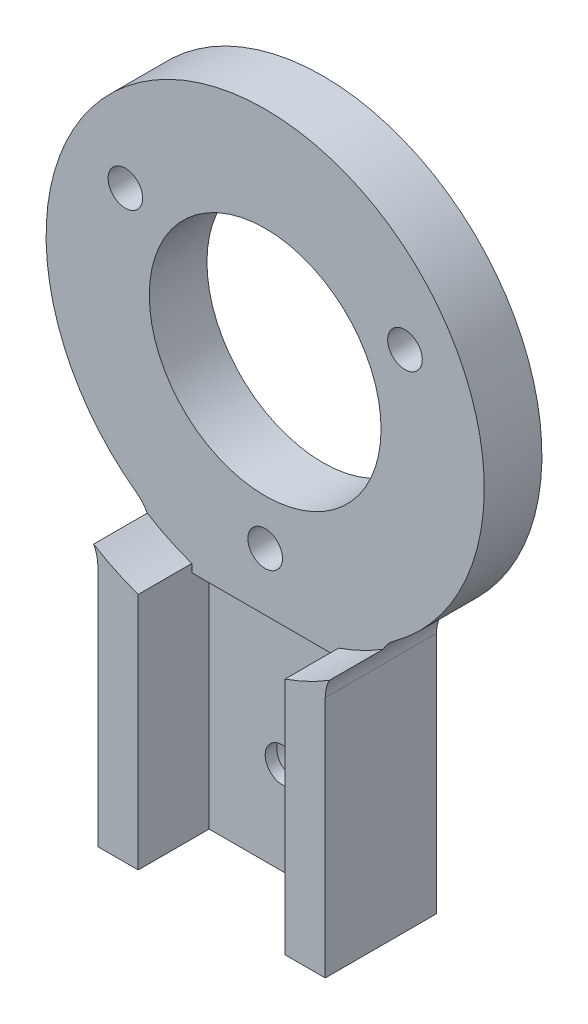
SolidWorks part; units mm, degrees
ref_plane "Front Plane" through (0, 0, 0) normal (0, 0, 1) x (1, 0, 0)
ref_plane "Top Plane" through (0, 0, 0) normal (0, 1, 0) x (1, 0, 0)
ref_plane "Right Plane" through (0, 0, 0) normal (1, 0, 0) x (0, 0, -1)
sketch "Sketch1" plane through (0, 0, 0) normal (0, 0, 1) x (1, 0, 0)
  line L0 (0, -19) -> (0, -39) construction
  line L1 (9.86, -39) -> (-9.86, -39)
  line L2 (-9.86, -39) -> (-9.86, -16.2413)
  line L3 (9.86, -39) -> (9.86, -16.2413)
  line L4 (6.36, -30.5545) -> (-6.36, -30.5545) construction
  circle A0 centre (0, 0) radius 19 construction
  circle A1 centre (0, 0) radius 10
  arc A2 (-9.86, -16.2413) -> (9.86, -16.2413) centre (0, 0) cw
  point P11 (0, -39)
  point P14 (0, -30.5545)
  dimension "D1" = 38
  dimension "D2" = 20
  dimension "D3" = 12.72
  dimension "D4" = 3.5
  dimension "D5" = 20
extrude "Boss-Extrude1" add sketch "Sketch1" along normal blind 5
sketch "Sketch6" plane through (0, 0, 5) normal (0, 0, 1) x (1, 0, 0)
  circle A0 centre (0, 0) radius 19 construction
sketch "Sketch5" plane through (0, -39, 0) normal (0, -1, 0) x (1, 0, 0)
  line L1 (0, 0) -> (0, 3.5) construction
  line L2 (-9.86, 0) -> (9.86, 0) construction
  line L3 (6.36, 3.5) -> (-6.36, 3.5)
  line L4 (-6.36, 3.5) -> (-6.36, 5)
  line L5 (-9.86, 5) -> (9.86, 5) construction
  line L6 (-6.36, 5) -> (6.36, 5)
  line L7 (6.36, 5) -> (6.36, 3.5)
  dimension "D1" = 3.5
  dimension "D2" = 12.72
extrude "Cut-Extrude1" cut sketch "Sketch5" against normal blind 20
sketch "Sketch7" plane through (0, -39, 0) normal (0, -1, 0) x (1, 0, 0)
  line L0 (0, 3.5) -> (0, 9.86) construction
  line L1 (-6.36, 3.5) -> (6.36, 3.5) construction
  dimension "D1" = 6.36
ref_plane "Plane2" through (0, 0, 9.86) normal (0, 0, 1) x (1, 0, 0)
sketch "Sketch8" plane through (0, 0, 9.86) normal (0, 0, 1) x (1, 0, 0)
  line L0 (0, -39) -> (0, 0) construction
sketch "Sketch18" plane through (0, 0, 5) normal (0, 0, 1) x (1, 0, 0)
  line L0 (0, -14) -> (0, 0) construction
  line L1 (0, 0) -> (-12.1244, 7) construction
  line L3 (12.1244, 7) -> (0, 0) construction
  circle A0 centre (0, 0) radius 14 construction
  circle A1 centre (0, -14) radius 1.5
  circle A2 centre (-12.1244, 7) radius 1.5
  circle A3 centre (12.1244, 7) radius 1.5
  dimension "D1" = 28
  dimension "D2" = 3
  dimension "D3" = 120
  dimension "D4" = 120
extrude "Cut-Extrude6" cut sketch "Sketch18" against normal through all
sketch "Sketch10" plane through (0, 0, 5) normal (0, 0, 1) x (1, 0, 0)
  line L0 (9.86, -39) -> (9.86, -16.2413) construction
  line L1 (-9.86, -39) -> (-6.36, -39)
  line L2 (-9.86, -39) -> (-9.86, -19)
  line L3 (-9.86, -19) -> (-6.36, -19)
  line L4 (-6.36, -39) -> (-6.36, -19)
  line L5 (6.36, -39) -> (9.86, -39)
  line L6 (6.36, -39) -> (6.36, -19)
  line L7 (6.36, -19) -> (9.86, -19)
  line L8 (9.86, -39) -> (9.86, -19)
extrude "Boss-Extrude3" add sketch "Sketch10" along normal offset from surface (4.65 mm away) 9.65 up to face at (13.6244, 7, 0)
sketch "Sketch15" plane through (0, 0, 0) normal (0, 0, -1) x (-1, 0, 0)
  circle A0 centre (0, -14) radius 3
  circle A1 centre (-12.1244, 7) radius 3
  circle A2 centre (12.1244, 7) radius 3
  dimension "D1" = 6
extrude "Cut-Extrude4" cut sketch "Sketch15" against normal blind 2.5
sketch "Sketch19" plane through (0, 0, 0) normal (0, 0, -1) x (-1, 0, 0)
  circle A0 centre (0, 0) radius 10.05
  dimension "D1" = 20.1
extrude "Cut-Extrude7" cut sketch "Sketch19" against normal through all
sketch "Sketch23" plane through (0, 0, 5) normal (0, 0, 1) x (1, 0, 0)
  line L0 (9.86, -16.6785) -> (9.86, -19)
  line L1 (9.86, -19) -> (6.36, -19)
  line L2 (6.36, -19) -> (6.36, -18.3014)
  arc A0 (6.36, -18.3014) -> (9.86, -16.6785) centre (0, 0) ccw
  dimension "D1" = 38.75
extrude "Boss-Extrude6" add sketch "Sketch23" along normal up to surface (4.65 mm away) up to face at (8.11, -29, 9.65)
mirror "Mirror1" about plane through (0, 0, 0) normal (1, 0, 0) of "Boss-Extrude6"
sketch "Sketch24" plane through (0, 0, 0) normal (0, 0, -1) x (-1, 0, 0)
  line L0 (0, -39) -> (0, 0) construction
  line L1 (0, -14) -> (0, -31) construction
  line L2 (9.86, -39) -> (-9.86, -39) construction
  circle A0 centre (0, -31) radius 1.5
  circle A2 centre (0, -14) radius 1.5 construction
  dimension "D1" = 8
extrude "Cut-Extrude8" cut sketch "Sketch24" against normal blind 7
sketch "Sketch25" plane through (0, 0, 0) normal (0, 0, -1) x (-1, 0, 0)
  circle A0 centre (0, -31) radius 3
  circle A1 centre (0, -14) radius 3 construction
extrude "Cut-Extrude9" cut sketch "Sketch25" against normal up to surface (2.5 mm away) up to face at (-3, -14, 2.5)
fillet "Fillet5" radius 3.175 2 edges at (9.86, -16.2413, 2.5) (-9.86, -16.2413, 2.5)
sketch "Sketch26" plane through (0, 0, 3.5) normal (0, 0, 1) x (1, 0, 0)
  line L1 (-6.36, -19) -> (-1.61, -19)
  line L2 (-6.36, -19) -> (-6.36, -23.75)
  line L3 (-6.36, -23.75) -> (-1.61, -23.75)
  line L4 (-1.61, -19) -> (-1.61, -23.75)
  line L6 (6.36, -19) -> (1.61, -19)
  line L7 (6.36, -19) -> (6.36, -23.75)
  line L8 (6.36, -23.75) -> (1.61, -23.75)
  line L9 (1.61, -19) -> (1.61, -23.75)
  dimension "D1" = 4.75
